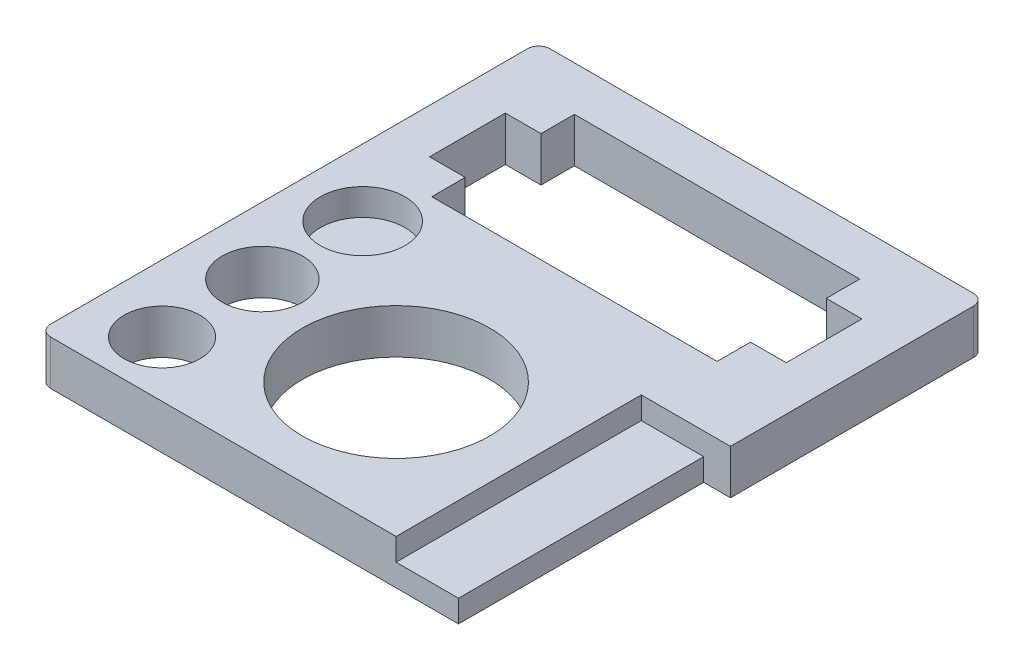
SolidWorks part; units mm, degrees
ref_plane "Plan de face" through (0, 0, 0) normal (0, 0, 1) x (1, 0, 0)
ref_plane "Plan de dessus" through (0, 0, 0) normal (0, 1, 0) x (1, 0, 0)
ref_plane "Plan de droite" through (0, 0, 0) normal (1, 0, 0) x (0, 0, -1)
sketch "Esquisse1" plane through (0, 0, 0) normal (0, 1, 0) x (1, 0, 0)
  line L0 (0, 14.4) -> (0, 8) construction
  line L1 (-6.4, 14.4) -> (6.4, 14.4)
  line L2 (-6.4, 14.4) -> (-6.4, 8)
  line L3 (-6.4, 8) -> (6.4, 8)
  line L4 (6.4, 14.4) -> (6.4, 8)
  line L5 (-8, 12.9) -> (-6.4, 12.9)
  line L6 (-8, 12.9) -> (-8, 9.5)
  line L7 (-8, 9.5) -> (-6.4, 9.5)
  line L8 (-6.4, 12.9) -> (-6.4, 9.5)
  line L9 (6.4, 12.9) -> (6.4, 9.5)
  line L10 (8, 9.5) -> (6.4, 9.5)
  line L11 (8, 12.9) -> (8, 9.5)
  line L12 (8, 12.9) -> (6.4, 12.9)
  line L14 (-10, 16.4) -> (10, 16.4)
  line L15 (-10, 16.4) -> (-10, -6)
  line L16 (-10, -6) -> (10, -6)
  line L17 (10, 16.4) -> (10, -6)
  line L18 (10, -6) -> (6, -6)
  line L19 (10, -6) -> (10, 5)
  line L20 (10, 5) -> (6, 5)
  line L21 (6, -6) -> (6, 5)
  circle A0 centre (0, 0) radius 4.2
  circle A1 centre (-7, -3.5) radius 1.7
  circle A2 centre (-7, 1) radius 1.8
  point P6 (0, 8)
  point P7 (-6.4, 11.2)
  point P12 (-6.4, 11.2)
  point P19 (0, -4.2)
  point P32 (8, 5)
  dimension "D6" = 8.4
  dimension "D11" = 3.4
  dimension "D12" = 2.5
  dimension "D13" = 3
  dimension "D14" = 3.6
  dimension "D15" = 3
  dimension "D16" = 7
  dimension "D17" = 6
  dimension "D1" = 8
  dimension "D2" = 6.4
  dimension "D3" = 12.8
  dimension "D4" = 1.6
  dimension "D5" = 3.4
  dimension "D7" = 2
  dimension "D8" = 2
  dimension "D9" = 2
  dimension "D10" = 6
  dimension "D18" = 11
extrude "Boss.-Extru.1" add sketch "Esquisse1" along normal blind 2 contours L17 L14 L15 L16 A0 L12 L11 L10 L4 L3 L2 L7 L6 L5 L1
sketch "Esquisse2" plane through (0, 2, 0) normal (0, 1, 0) x (1, 0, 0)
  line L0 (-6.4, 8) -> (6.4, 8) construction
  line L1 (-10, 16.4) -> (-10, -6) construction
  circle A0 centre (-7, 5.5) radius 1.9
  dimension "D1" = 3.8
  dimension "D2" = 2.5
  dimension "D3" = 3
extrude "Enlèv. mat.-Extru.1" cut sketch "Esquisse2" against normal blind 1.2
sketch "Esquisse4" plane through (0, 0, 0) normal (0, -1, 0) x (1, 0, 0)
  line L0 (-10, 6) -> (6, 6) construction
  line L1 (6, -5) -> (8.8, -5)
  line L2 (6, -5) -> (6, 6)
  line L3 (6, 6) -> (8.8, 6)
  line L4 (8.8, -5) -> (8.8, 6)
  dimension "D1" = 2.8
extrude "Boss.-Extru.3" add sketch "Esquisse4" against normal blind 1
fillet "Congé1" radius 0.5 3 edges at (10, 1, -16.4) (-10, 1, 6) (-10, 1, -16.4)
